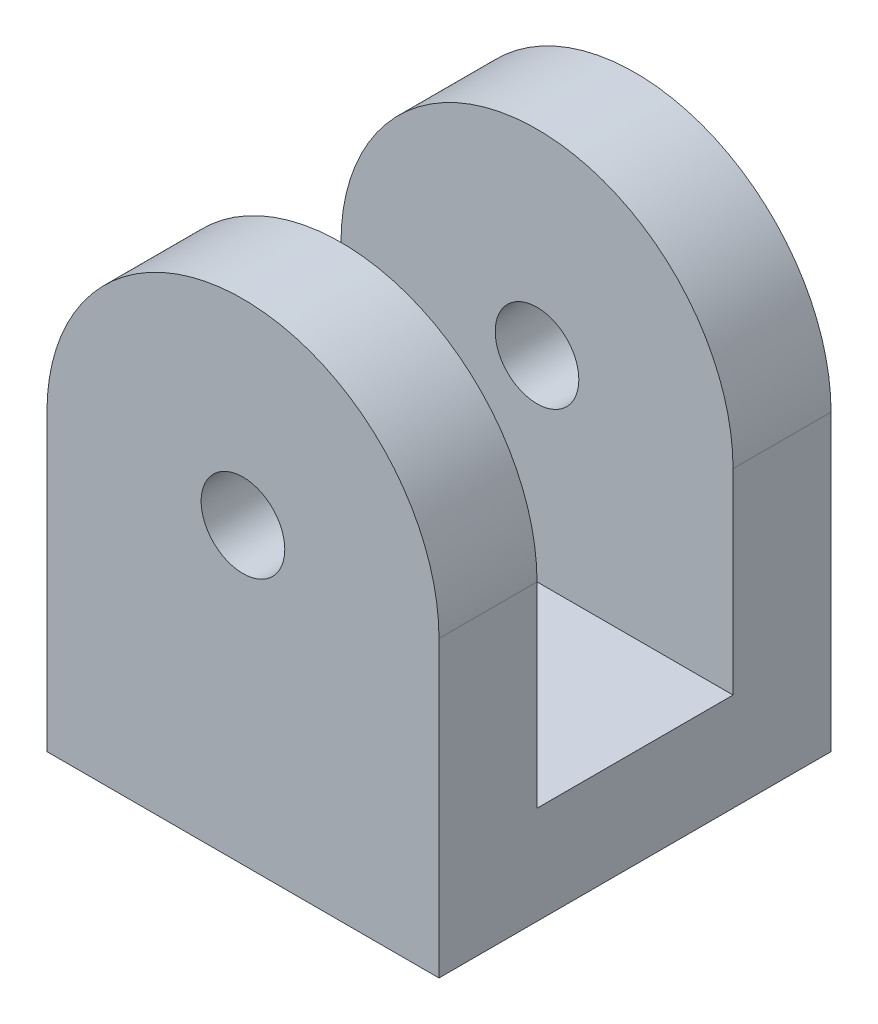
SolidWorks part; units mm, degrees
ref_plane "Front Plane" through (0, 0, 0) normal (0, 0, 1) x (1, 0, 0)
ref_plane "Top Plane" through (0, 0, 0) normal (0, 1, 0) x (1, 0, 0)
ref_plane "Right Plane" through (0, 0, 0) normal (1, 0, 0) x (0, 0, -1)
sketch "Sketch1" plane through (0, 0, 0) normal (0, 0, 1) x (1, 0, 0)
  line L5 (-7.5, -1.875) -> (7.5, -1.875)
  line L6 (-7.5, -1.875) -> (-7.5, 1.875)
  line L7 (-7.5, 1.875) -> (7.5, 1.875)
  line L8 (7.5, -1.875) -> (7.5, 1.875)
  line L9 (-7.5, -1.875) -> (7.5, 1.875) construction
  line L10 (-7.5, 1.875) -> (7.5, -1.875) construction
  point P0 (0, 0)
  point P1 (0, 0)
  dimension "D1" = 3.75
  dimension "D2" = 15
extrude "Boss-Extrude1" add sketch "Sketch1" along normal blind 7.5
sketch "Sketch2" plane through (0, 1.875, 0) normal (0, 1, 0) x (1, 0, 0)
  line L0 (7.5, -7.5) -> (7.5, 0) construction
  line L1 (-7.5, -7.5) -> (7.5, -7.5)
  line L2 (-7.5, -7.5) -> (-7.5, -3.75)
  line L3 (-7.5, -3.75) -> (7.5, -3.75)
  line L4 (7.5, -7.5) -> (7.5, -3.75)
  dimension "D1" = 3.75
extrude "Boss-Extrude2" add sketch "Sketch2" along normal blind 15
sketch "Sketch3" plane through (0, 0, 7.5) normal (0, 0, 1) x (1, 0, 0)
  line L0 (-7.5, 16.875) -> (7.5, 16.875) construction
  line L2 (-7.5, 9.375) -> (7.5, 9.375)
  line L3 (-7.5, 9.375) -> (-7.5, -1.875)
  line L4 (-7.5, -1.875) -> (7.5, -1.875)
  line L5 (7.5, 9.375) -> (7.5, -1.875)
  line L7 (7.5, -1.875) -> (7.5, 16.875) construction
  circle A0 centre (0, 9.375) radius 1.6
  arc A2 (7.5, 9.375) -> (-7.5, 9.375) centre (0, 9.375) ccw
  dimension "D1" = 3.2
  dimension "D2" = 7.5
extrude "Cut-Extrude1" cut sketch "Sketch3" against normal up to surface (3.75 mm away) and the other way through all
mirror "Mirror1" about plane through (0, 0, 0) normal (0, 0, -1) of bodies 104 102
